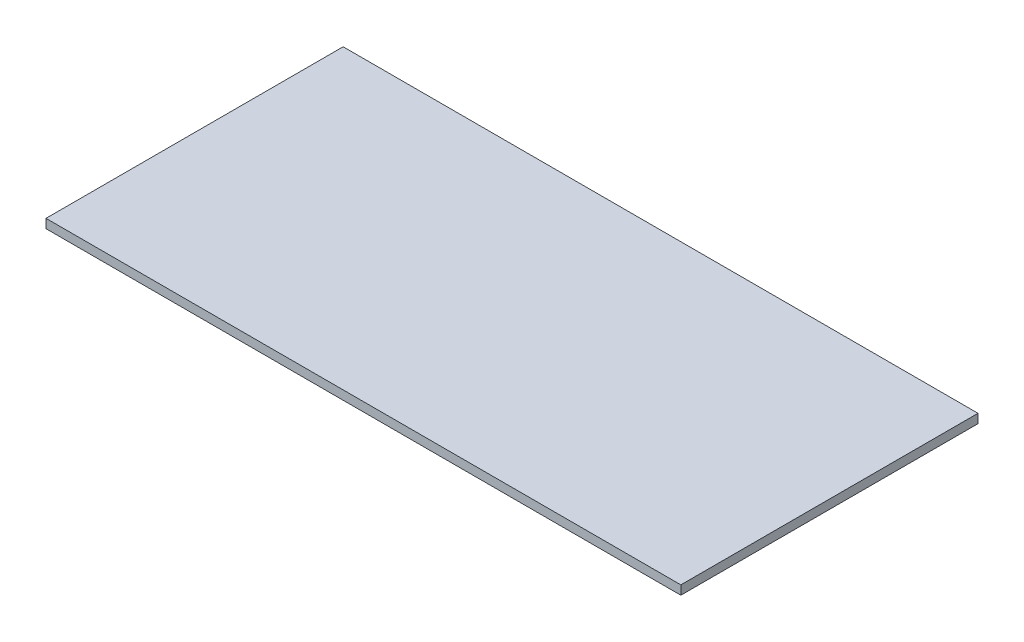
SolidWorks part; units mm, degrees
ref_plane "Front Plane" through (0, 0, 0) normal (0, 0, 1) x (1, 0, 0)
ref_plane "Top Plane" through (0, 0, 0) normal (0, 1, 0) x (1, 0, 0)
ref_plane "Right Plane" through (0, 0, 0) normal (1, 0, 0) x (0, 0, -1)
sketch "Sketch1" plane through (0, 0, 0) normal (0, 1, 0) x (1, 0, 0)
  line L1 (-634.5, -297) -> (634.5, -297)
  line L2 (-634.5, -297) -> (-634.5, 297)
  line L3 (-634.5, 297) -> (634.5, 297)
  line L4 (634.5, -297) -> (634.5, 297)
  line L5 (-634.5, -297) -> (634.5, 297) construction
  line L6 (-634.5, 297) -> (634.5, -297) construction
  point P0 (0, 0)
  dimension "D1" = 1269
  dimension "D2" = 594
extrude "Boss-Extrude1" add sketch "Sketch1" along normal blind 18
